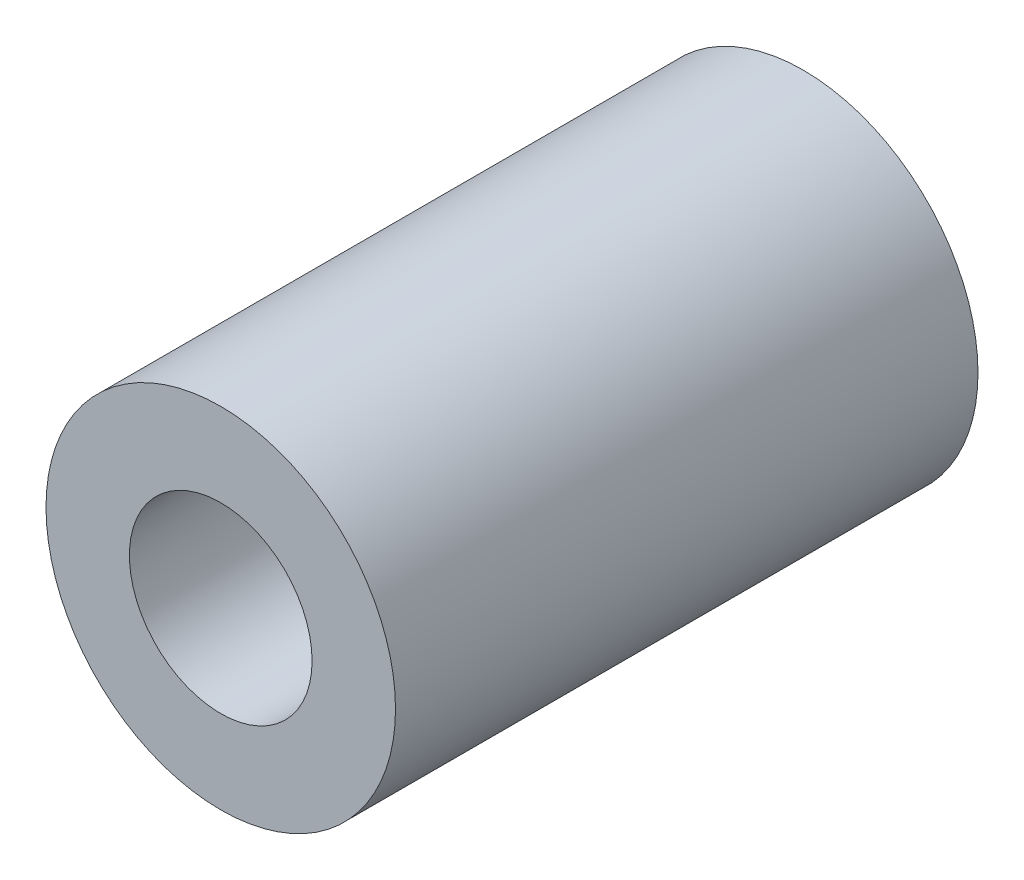
SolidWorks part; units mm, degrees
material "6061-T6 (SS)"
ref_plane "Front Plane" through (0, 0, 0) normal (0, 0, 1) x (1, 0, 0)
ref_plane "Top Plane" through (0, 0, 0) normal (0, 1, 0) x (1, 0, 0)
ref_plane "Right Plane" through (0, 0, 0) normal (1, 0, 0) x (0, 0, -1)
sketch "Sketch1" plane through (0, 0, 0) normal (0, 0, 1) x (1, 0, 0)
  circle A0 centre (0, 0) radius 2.4892
  circle A1 centre (0, 0) radius 4.7625
  dimension "D1" = 9.525
  dimension "D2" = 4.9784
extrude "Boss-Extrude1" add sketch "Sketch1" along normal blind 15.875 contours A1 A0
